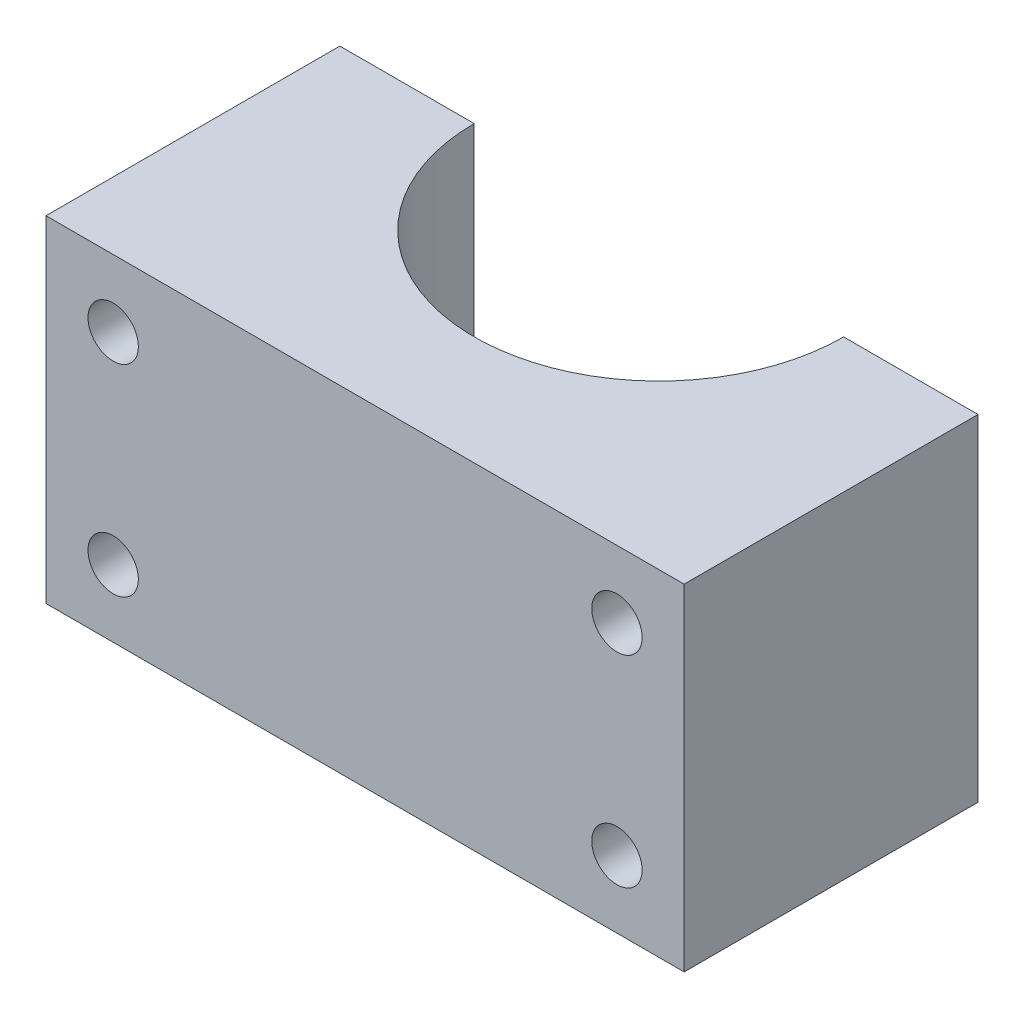
SolidWorks part; units mm, degrees
material "Nailon 101"
ref_plane "Alzado" through (0, 0, 0) normal (0, 0, 1) x (1, 0, 0)
ref_plane "Planta" through (0, 0, 0) normal (0, 1, 0) x (1, 0, 0)
ref_plane "Vista lateral" through (0, 0, 0) normal (1, 0, 0) x (0, 0, -1)
sketch "Croquis1" plane through (0, 0, 0) normal (0, 1, 0) x (1, 0, 0)
  line L0 (-19, 0) -> (-11, 0)
  line L1 (19, 0) -> (19, -17.5)
  line L2 (19, -17.5) -> (-19, -17.5)
  line L3 (-19, -17.5) -> (-19, 0)
  line L4 (11, 0) -> (19, 0)
  line L5 (0, -17.5) -> (0, 0) construction
  arc A0 (-11, 0) -> (11, 0) centre (0, 0) ccw
  dimension "D1" = 22
  dimension "D2" = 17.5
  dimension "D3" = 38
extrude "Saliente-Extruir1" add sketch "Croquis1" along normal blind 20
sketch "Croquis2" plane through (0, 0, 17.5) normal (0, 0, 1) x (1, 0, 0)
  line L0 (0, 0) -> (0, 20) construction
  line L1 (-19, 20) -> (19, 20) construction
  line L2 (-19, 0) -> (19, 0) construction
  line L3 (15, 4) -> (-15, 4) construction
  line L4 (15, 4) -> (15, 16) construction
  line L5 (15, 16) -> (-15, 16) construction
  line L6 (-15, 4) -> (-15, 16) construction
  circle A0 centre (-15, 16) radius 1.5
  circle A1 centre (-15, 4) radius 1.5
  circle A2 centre (15, 4) radius 1.5
  circle A3 centre (15, 16) radius 1.5
  point P9 (0, 4)
  dimension "D4" = 3
  dimension "D1" = 4
  dimension "D2" = 4
  dimension "D3" = 30
extrude "Cortar-Extruir1" cut sketch "Croquis2" against normal through all
